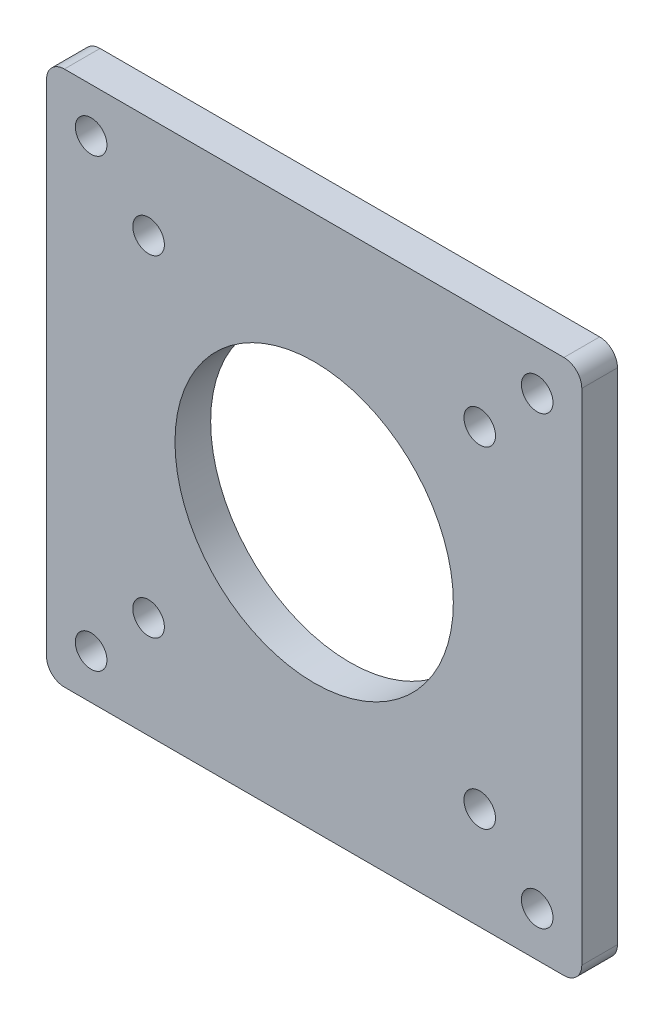
SolidWorks part; units mm, degrees
ref_plane "Front Plane" through (0, 0, 0) normal (0, 0, 1) x (1, 0, 0)
ref_plane "Top Plane" through (0, 0, 0) normal (0, 1, 0) x (1, 0, 0)
ref_plane "Right Plane" through (0, 0, 0) normal (1, 0, 0) x (0, 0, -1)
sketch "Sketch1" plane through (0, 0, 0) normal (0, 0, 1) x (1, 0, 0)
  line L0 (23.755, 28.2) -> (-23.755, 28.2) construction
  line L1 (-30.74, 30.74) -> (30.74, 30.74)
  line L2 (-30.74, 30.74) -> (-30.74, -30.74)
  line L3 (-30.74, -30.74) -> (30.74, -30.74)
  line L4 (30.74, 30.74) -> (30.74, -30.74)
  line L5 (-28.2, 23.755) -> (-28.2, -23.755) construction
  line L6 (28.2, -23.755) -> (28.2, 23.755) construction
  line L7 (-30.74, 0) -> (30.74, 0) construction
  line L8 (-23.755, -28.2) -> (23.755, -28.2) construction
  line L9 (0, 30.74) -> (0, -30.74) construction
  circle A0 centre (-23.57, 23.57) radius 2.2479
  circle A1 centre (-23.57, 23.57) radius 2.2479 construction
  circle A2 centre (-23.57, -23.57) radius 2.2479
  circle A3 centre (23.57, -23.57) radius 2.2479
  circle A6 centre (0, 0) radius 19.812
  circle A7 centre (0, 0) radius 19.812
  circle A8 centre (23.57, 23.57) radius 2.2479
  dimension "D2" = 2.54
  dimension "D3" = 2.54
  dimension "D1" = 2.54
  dimension "D4" = 2.54
  dimension "D5" = 0.762
extrude "Boss-Extrude1" add sketch "Sketch1" along normal blind 5.08
fillet "Fillet1" radius 2.54 4 edges at (30.74, -30.74, 2.54) (-30.74, -30.74, 2.54) (-30.74, 30.74, 2.54) (30.74, 30.74, 2.54)
sketch "Sketch7" plane through (0, 0, 0) normal (0, 0, -1) x (-1, 0, 0)
  line L0 (0, 0) -> (-40.1051, 40.1051) construction
  line L1 (0, -41.443) -> (0, 41.443) construction
  line L2 (-27.2599, 36.2401) -> (-36.2401, 27.2599) construction
  line L3 (-27.2599, 36.2401) -> (-21.7597, 30.74)
  line L5 (-28.2, 30.74) -> (28.2, 30.74) construction
  line L6 (-21.7597, 30.74) -> (-30.74, 21.7597)
  line L8 (-30.74, -28.2) -> (-30.74, 28.2) construction
  line L9 (-30.74, 21.7597) -> (-36.2401, 27.2599)
  line L10 (30.74, 0) -> (-30.74, 0) construction
  line L11 (30.74, 28.2) -> (30.74, -28.2) construction
  line L13 (27.2599, 36.2401) -> (36.2401, 27.2599) construction
  line L14 (0, 0) -> (40.1051, 40.1051) construction
  line L15 (30.74, 21.7597) -> (36.2401, 27.2599)
  line L16 (21.7597, 30.74) -> (30.74, 21.7597)
  line L17 (27.2599, 36.2401) -> (21.7597, 30.74)
  line L18 (0, 0) -> (40.1051, -40.1051) construction
  line L19 (27.2599, -36.2401) -> (36.2401, -27.2599) construction
  line L20 (-27.2599, -36.2401) -> (-36.2401, -27.2599) construction
  line L21 (0, 0) -> (-40.1051, -40.1051) construction
  line L22 (27.2599, -36.2401) -> (21.7597, -30.74)
  line L23 (21.7597, -30.74) -> (30.74, -21.7597)
  line L24 (30.74, -21.7597) -> (36.2401, -27.2599)
  line L25 (-30.74, -21.7597) -> (-36.2401, -27.2599)
  line L26 (-21.7597, -30.74) -> (-30.74, -21.7597)
  line L27 (-27.2599, -36.2401) -> (-21.7597, -30.74)
  arc A0 (-27.2599, 36.2401) -> (-36.2401, 27.2599) centre (-31.75, 31.75) ccw
  arc A3 (27.2599, 36.2401) -> (36.2401, 27.2599) centre (31.75, 31.75) cw
  arc A4 (27.2599, -36.2401) -> (36.2401, -27.2599) centre (31.75, -31.75) ccw
  arc A5 (-27.2599, -36.2401) -> (-36.2401, -27.2599) centre (-31.75, -31.75) cw
  point P9 (-23.57, 23.57)
  point P23 (23.57, 23.57)
  point P41 (23.57, -23.57)
  point P42 (-23.57, -23.57)
  dimension "D1" = 31.75
  dimension "D2" = 6.35
extrude "Boss-Extrude2" add sketch "Sketch7" against normal through all
sketch "Sketch8" plane through (0, 0, 0) normal (0, 0, -1) x (-1, 0, 0)
  line L0 (30.74, 21.7597) -> (30.74, -21.7597) construction
  line L1 (-38.1, -38.1) -> (38.1, -38.1)
  line L2 (-38.1, -38.1) -> (-38.1, 38.1)
  line L3 (-38.1, 38.1) -> (38.1, 38.1)
  line L4 (38.1, -38.1) -> (38.1, 38.1)
  line L5 (-38.1, -38.1) -> (38.1, 38.1) construction
  line L6 (-38.1, 38.1) -> (38.1, -38.1) construction
  line L7 (-30.74, -30.74) -> (30.74, -30.74)
  line L8 (-30.74, -30.74) -> (-30.74, 30.74)
  line L9 (-30.74, 30.74) -> (30.74, 30.74)
  line L10 (30.74, -30.74) -> (30.74, 30.74)
  line L11 (-30.74, -30.74) -> (30.74, 30.74) construction
  line L12 (-30.74, 30.74) -> (30.74, -30.74) construction
  line L13 (21.7597, -30.74) -> (-21.7597, -30.74) construction
  arc A1 (36.2401, 27.2599) -> (27.2599, 36.2401) centre (31.75, 31.75) ccw construction
  point P0 (0, 0)
extrude "Boss-Extrude3" add sketch "Sketch8" against normal through all
hole_wizard "#8 Clearance Hole1" positions "Sketch3" profile "Sketch2" hole size "#8" standard "ANSI Inch" end condition through all
sketch "Sketch3" plane through (0, 0, 0) normal (0, 0, -1) x (-1, 0, 0)
  line L0 (0, 0) -> (23.57, 23.57) construction
  line L1 (0, 0) -> (-38.1, 0) construction
  line L2 (-38.1, 38.1) -> (-38.1, -38.1) construction
  line L4 (0, 0) -> (0, -38.1) construction
  line L5 (-38.1, -38.1) -> (38.1, -38.1) construction
  point P76 (31.75, 31.75)
  point P94 (0, 0)
  point P107 (0, 0)
  point P124 (31.75, -31.75)
  point P128 (-31.75, -31.75)
  point P129 (-31.75, 31.75)
  dimension "D1" = 31.75
sketch "Sketch2" plane through (-31.75, 31.75, 0) normal (1, 0, 0) x (0, 1, 0)
  line L0 (0, 0) -> (0, 5.08)
  line L1 (0, 5.08) -> (2.2479, 5.08)
  line L2 (2.2479, 5.08) -> (2.2479, 0)
  line L5 (2.2479, 0) -> (0, 0)
  line L11 (0, -6.35) -> (0, 107.95) construction
  dimension "Thru Hole Dia." = 4.4958
  dimension "Thru Hole Depth" = 5.08
fillet "Fillet2" radius 2.54 4 edges at (-38.1, 38.1, 2.54) (-38.1, -38.1, 2.54) (38.1, -38.1, 2.54) (38.1, 38.1, 2.54)
